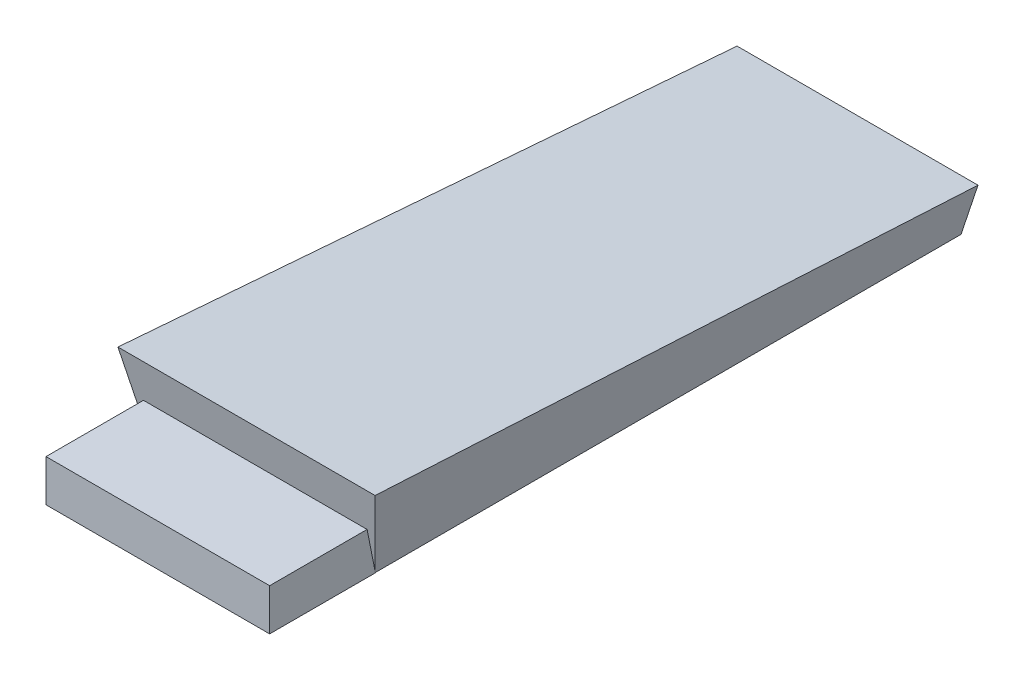
SolidWorks part; units mm, degrees
ref_plane "Front" through (0, 0, 0) normal (0, 0, 1) x (1, 0, 0)
ref_plane "Top" through (0, 0, 0) normal (0, 1, 0) x (1, 0, 0)
ref_plane "Right" through (0, 0, 0) normal (1, 0, 0) x (0, 0, -1)
sketch "Sketch1" plane through (0, 0, 0) normal (0, 1, 0) x (1, 0, 0)
  line L1 (-284.8524, 134.0482) -> (-81.6524, 134.0482)
  line L2 (-284.8524, 134.0482) -> (-284.8524, -234.2518)
  line L3 (-284.8524, -234.2518) -> (-81.6524, -234.2518)
  line L4 (-81.6524, 134.0482) -> (-81.6524, -234.2518)
  dimension "D1" = 368.3
  dimension "D2" = 203.2
extrude "Boss-Extrude4" add sketch "Sketch1" along normal blind 254 draft 11.25
ref_plane "Plane1" through (-82.7176, 0, 0) normal (1, 0, 0) x (0, 0, -1)
sketch "Sketch2" plane through (-82.7176, 0, 0) normal (1, 0, 0) x (0, 0, -1)
  line L0 (-183.7281, 254) -> (-191.905, 215.9)
  line L1 (-191.905, 215.9) -> (93.1494, 234.95)
  line L2 (93.1494, 234.95) -> (83.5244, 254)
  line L3 (83.5244, 254) -> (-183.7281, 254)
  line L4 (-234.1068, 0) -> (-191.905, 215.9)
  line L5 (-234.1068, 0) -> (147.4855, 0)
  line L6 (147.4855, 0) -> (93.1494, 234.95)
  dimension "D1" = 38.1
  dimension "D2" = 19.05
extrude "Cut-Extrude1" cut sketch "Sketch2" against normal blind 254 contours L5 L6 L1 L4
sketch "Sketch3" plane through (-82.7176, 0, 0) normal (1, 0, 0) x (0, 0, -1)
  line L0 (-183.7281, 254) -> (-231.9674, 254)
  line L1 (-231.9674, 254) -> (-231.9674, 234.95)
  line L2 (-231.9674, 234.95) -> (-187.5174, 234.95)
  line L3 (-183.7281, 254) -> (-191.2986, 215.9405) construction
  line L4 (-187.5174, 234.95) -> (-183.7281, 254)
  dimension "D1" = 44.45
  dimension "D2" = 19.05
extrude "Boss-Extrude5" add sketch "Sketch3" along normal blind 102 from offset 151.75 offset against normal yes
move or copy body "Body-Move/Copy1" bodies to move or copy 110 copy no rotation origin (-183.2524, 234.9703, 0) rotation axis (0, 0, 1) rotation angle 180
